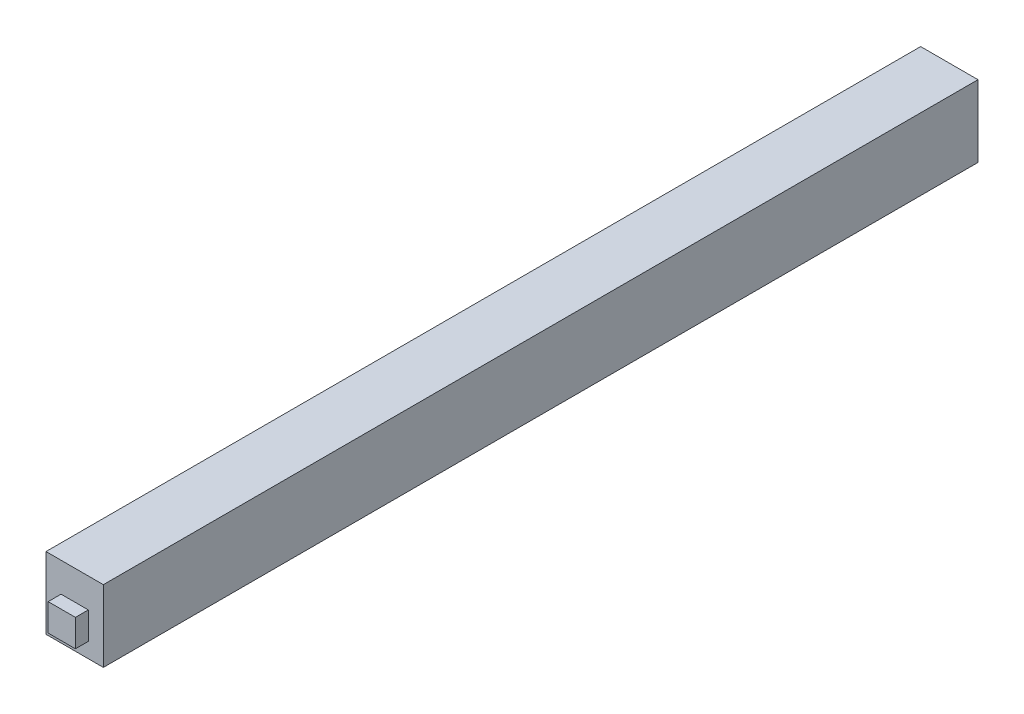
SolidWorks part; units mm, degrees
ref_plane "Front Plane" through (0, 0, 0) normal (0, 0, 1) x (1, 0, 0)
ref_plane "Top Plane" through (0, 0, 0) normal (0, 1, 0) x (1, 0, 0)
ref_plane "Right Plane" through (0, 0, 0) normal (1, 0, 0) x (0, 0, -1)
sketch "Sketch1" plane through (0, 0, 0) normal (0, 0, 1) x (1, 0, 0)
  line L1 (0, 0) -> (8, 0)
  line L2 (0, 0) -> (0, 10)
  line L3 (0, 10) -> (8, 10)
  line L4 (8, 0) -> (8, 10)
  dimension "D1" = 8
  dimension "D2" = 10
extrude "Boss-Extrude1" add sketch "Sketch1" along normal blind 122
sketch "Sketch2" plane through (0, 0, 0) normal (0, 0, -1) x (-1, 0, 0)
  line L0 (-4, 0) -> (-4, 4) construction
  line L1 (0, 0) -> (-8, 0) construction
  line L3 (-5.9, 2.1) -> (-2.1, 2.1)
  line L4 (-5.9, 2.1) -> (-5.9, 5.9)
  line L5 (-5.9, 5.9) -> (-2.1, 5.9)
  line L6 (-2.1, 2.1) -> (-2.1, 5.9)
  line L7 (-5.9, 2.1) -> (-2.1, 5.9) construction
  line L8 (-5.9, 5.9) -> (-2.1, 2.1) construction
  dimension "D1" = 4
  dimension "D2" = 3.8
  dimension "D3" = 3.8
extrude "Boss-Extrude2" add sketch "Sketch2" along normal blind 1.8
sketch "Sketch3" plane through (0, 0, 122) normal (0, 0, 1) x (1, 0, 0)
  line L0 (4, 0) -> (4, 4)
  line L1 (0, 0) -> (8, 0) construction
  line L3 (2.1, 2.1) -> (5.9, 2.1)
  line L4 (2.1, 2.1) -> (2.1, 5.9)
  line L5 (2.1, 5.9) -> (5.9, 5.9)
  line L6 (5.9, 2.1) -> (5.9, 5.9)
  line L7 (2.1, 2.1) -> (5.9, 5.9) construction
  line L8 (2.1, 5.9) -> (5.9, 2.1) construction
  dimension "D1" = 4
  dimension "D2" = 3.8
  dimension "D3" = 3.8
extrude "Boss-Extrude3" add sketch "Sketch3" along normal blind 1.8
